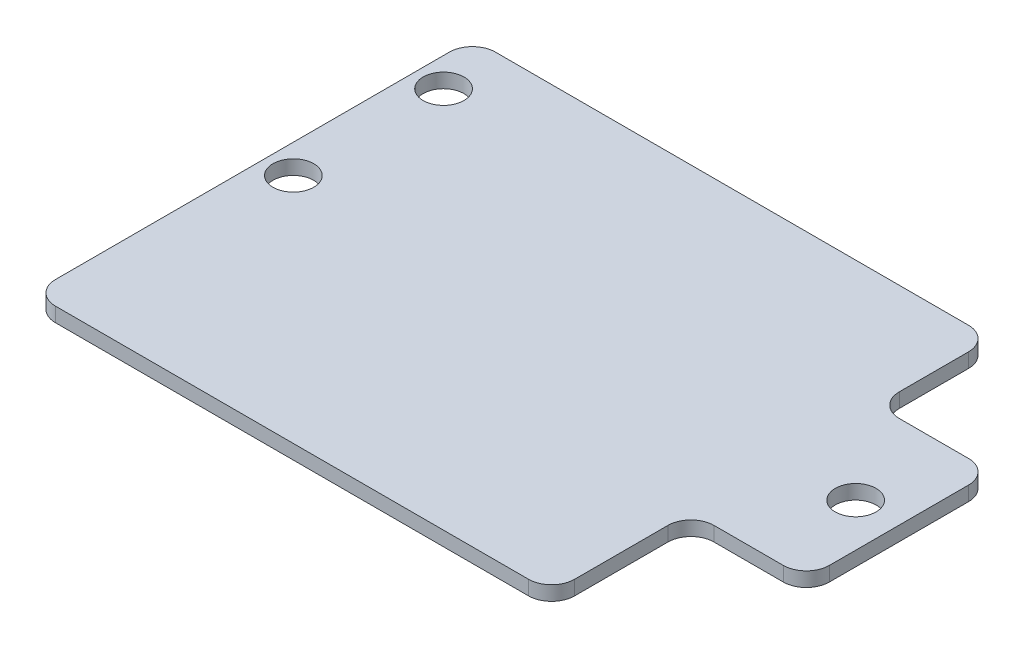
SolidWorks part; units mm, degrees
material "AISI Type A2 Tool Steel"
ref_plane "Front Plane" through (0, 0, 0) normal (0, 0, 1) x (1, 0, 0)
ref_plane "Top Plane" through (0, 0, 0) normal (0, 1, 0) x (1, 0, 0)
ref_plane "Right Plane" through (0, 0, 0) normal (1, 0, 0) x (0, 0, -1)
sketch "Sketch1" plane through (0, 0, 0) normal (0, 1, 0) x (1, 0, 0)
  line B0 (0, 0) -> (0, -48.4323)
  line B1 (0, -48.4323) -> (57.15, -48.4323)
  line B2 (57.15, -48.4323) -> (57.15, -33.0905)
  line B3 (57.15, -33.0905) -> (69.85, -33.0905)
  line B4 (69.85, -33.0905) -> (69.85, -12.7)
  line B5 (69.85, -12.7) -> (57.15, -12.7)
  line B6 (57.15, -12.7) -> (57.15, 0)
  line B7 (0, 0) -> (57.15, 0)
sketch_block_instance "Block-Armor-1"
sketch_block "Block-Armor" parameters "D1"=12.7
extrude "Boss-Extrude1" add sketch "Sketch1" along normal blind 1.5875
fillet "Fillet1" radius 2.54 8 edges at (0, 0.7937, 48.4323) (0, 0.7937, 0) (57.15, 0.7937, 0) (57.15, 0.7937, 48.4323) (69.85, 0.7937, 33.0905) (69.85, 0.7937, 12.7) (57.15, 0.7937, 33.0905) (57.15, 0.7937, 12.7)
sketch "Sketch2" plane through (0, 1.5875, 0) normal (0, 1, 0) x (1, 0, 0)
  line L0 (0, -2.54) -> (0, -45.8923) construction
  line L1 (69.85, -30.5505) -> (69.85, -15.24) construction
  line L2 (54.61, 0) -> (2.54, 0) construction
  circle A0 centre (3.175, -6.35) radius 2.2479
  circle A1 centre (3.175, -22.8854) radius 2.2479
  circle A2 centre (65.0748, -22.8854) radius 2.2479
  dimension "D1" = 4.4958
  dimension "D2" = 3.175
  dimension "D3" = 16.5354
  dimension "D4" = 4.7752
  dimension "D5" = 6.35
extrude "Cut-Extrude1" cut sketch "Sketch2" against normal through all
